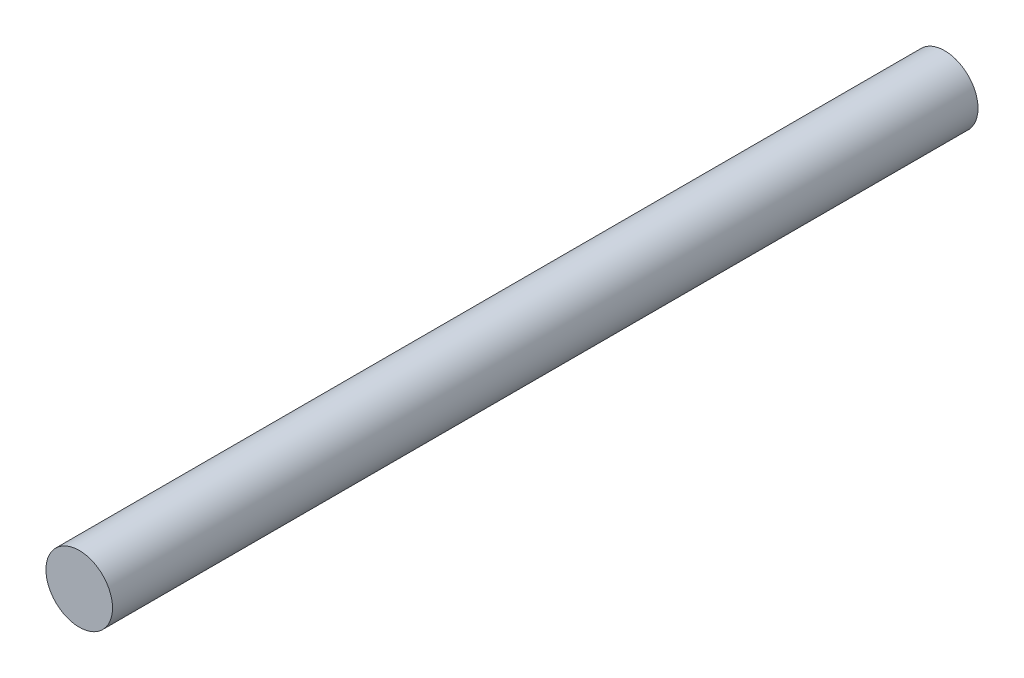
SolidWorks part; units mm, degrees
material "AISI 1020 Steel, Cold Rolled"
ref_plane "Front Plane" through (0, 0, 0) normal (0, 0, 1) x (1, 0, 0)
ref_plane "Top Plane" through (0, 0, 0) normal (0, 1, 0) x (1, 0, 0)
ref_plane "Right Plane" through (0, 0, 0) normal (1, 0, 0) x (0, 0, -1)
sketch "Sketch2" plane through (0, 0, 0) normal (0, 0, 1) x (1, 0, 0)
  circle A0 centre (0, 0) radius 6.35
  dimension "D1" = 12.7
extrude "Boss-Extrude1" add sketch "Sketch2" along normal blind 165.1
sketch "Sketch3" [suppressed] plane through (0, 0, 220.98) normal (0, 0, 1) x (1, 0, 0)
  circle A0 centre (0, 0) radius 6.35
extrude "Cut-Extrude1" [suppressed] cut sketch "Sketch3" against normal blind 26.416
sketch "Sketch4" [suppressed] plane through (0, 0, 194.564) normal (0, 0, 1) x (1, 0, 0)
  circle A0 centre (0, 0) radius 3.175
  dimension "D1" = 6.35
extrude "Boss-Extrude2" [suppressed] add sketch "Sketch4" along normal blind 26.416
sketch "Sketch5" [suppressed] plane through (0, 0, 0) normal (0, 0, -1) x (-1, 0, 0)
  circle A0 centre (0, 0) radius 6.35
extrude "Cut-Extrude2" [suppressed] cut sketch "Sketch5" against normal blind 26.416
sketch "Sketch6" [suppressed] plane through (0, 0, 26.416) normal (0, 0, -1) x (-1, 0, 0)
  circle A0 centre (0, 0) radius 3.175
  dimension "D1" = 6.35
extrude "Boss-Extrude3" [suppressed] add sketch "Sketch6" along normal blind 26.416
sketch "Sketch7" [suppressed] plane through (0, 0, 0) normal (0, 0, -1) x (-1, 0, 0)
  circle A0 centre (0, 0) radius 14.231
extrude "Cut-Extrude3" [suppressed] cut sketch "Sketch7" against normal blind 27.432
sketch "Sketch8" [suppressed] plane through (0, 0, 27.432) normal (0, 0, -1) x (-1, 0, 0)
  circle A0 centre (0, 0) radius 3.175
  dimension "D1" = 6.35
extrude "Boss-Extrude4" [suppressed] add sketch "Sketch8" along normal blind 27.432
sketch "Sketch9" [suppressed] plane through (0, 0, 220.98) normal (0, 0, 1) x (1, 0, 0)
  circle A0 centre (0, 0) radius 8.8374
extrude "Cut-Extrude4" [suppressed] cut sketch "Sketch9" against normal blind 27.432
sketch "Sketch10" [suppressed] plane through (0, 0, 193.548) normal (0, 0, 1) x (1, 0, 0)
  circle A0 centre (0, 0) radius 3.175
  dimension "D1" = 6.35
extrude "Boss-Extrude5" [suppressed] add sketch "Sketch10" along normal blind 27.432
